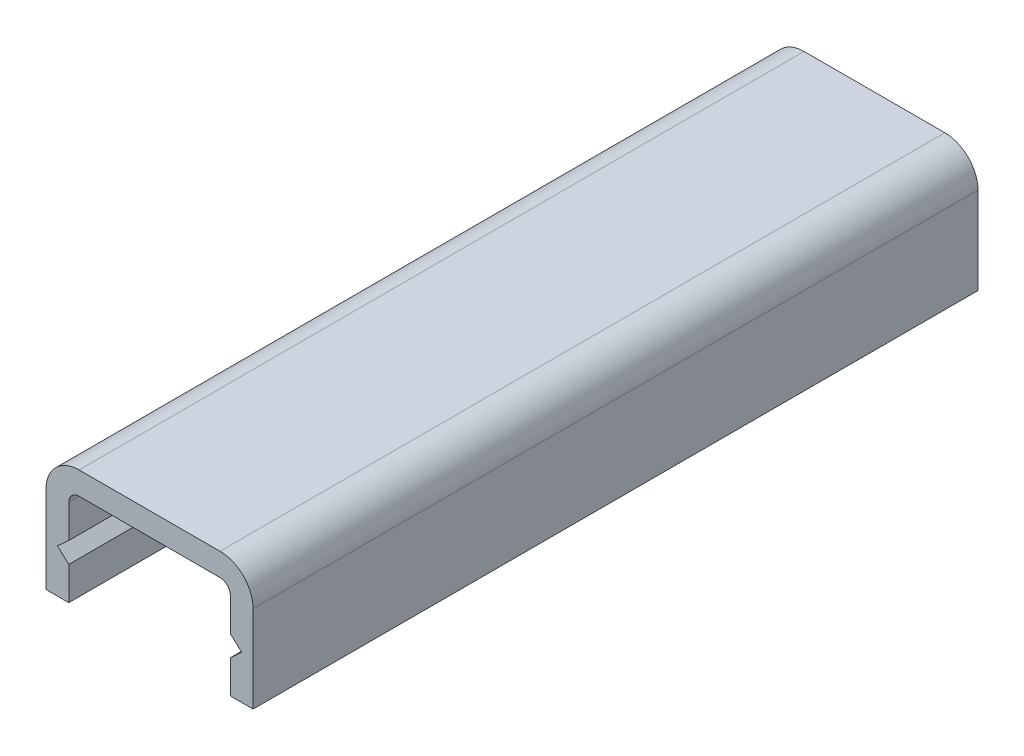
SolidWorks part; units mm, degrees
ref_plane "Plan de face" through (0, 0, 0) normal (0, 0, 1) x (1, 0, 0)
ref_plane "Plan de dessus" through (0, 0, 0) normal (0, 1, 0) x (1, 0, 0)
ref_plane "Plan de droite" through (0, 0, 0) normal (1, 0, 0) x (0, 0, -1)
sketch "Esquisse1" plane through (0, 0, 0) normal (0, 0, 1) x (1, 0, 0)
  line L0 (1.6, 5.8) -> (8.4, 5.8)
  line L1 (10, 4.2) -> (10, 0)
  line L2 (10, 0) -> (8.9, 0)
  line L3 (0, 4.2) -> (0, 0)
  line L4 (1.1, 2.6) -> (8.9, 2.6) construction
  line L5 (8.9, 4.2) -> (8.9, 2.6)
  line L6 (1.6, 4.7) -> (8.4, 4.7)
  line L7 (1.1, 4.2) -> (1.1, 2.6)
  line L8 (0, 0) -> (1.1, 0)
  line L9 (8.9, 4.7) -> (8.9, 1.1) construction
  line L10 (0, 5.8) -> (10, 5.8) construction
  line L11 (0, 5.8) -> (0, 0) construction
  line L12 (1.1, 4.7) -> (8.9, 4.7) construction
  line L13 (1.1, 4.7) -> (1.1, 0) construction
  line L14 (10, 5.8) -> (10, 0) construction
  line L15 (1.1, 1.6) -> (1.1, 0)
  line L16 (1.1, 1.6) -> (0.55, 2.1)
  line L17 (8.9, 1.6) -> (8.9, 0)
  line L18 (1.1, 2.6) -> (0.55, 2.1)
  line L19 (8.9, 2.6) -> (9.45, 2.1)
  line L20 (8.9, 1.6) -> (9.45, 2.1)
  line L21 (8.9, 1.1) -> (8.9, 1.1) construction
  line L22 (0.55, 2.1) -> (9.45, 2.1) construction
  line L23 (8.9, 1.6) -> (1.1, 1.6) construction
  line L24 (0, 0) -> (10, 0) construction
  arc A1 (1.6, 4.7) -> (1.1, 4.2) centre (1.6, 4.2) ccw
  arc A2 (8.9, 4.2) -> (8.4, 4.7) centre (8.4, 4.2) ccw
  arc A3 (8.4, 5.8) -> (10, 4.2) centre (8.4, 4.2) cw
  arc A4 (0, 4.2) -> (1.6, 5.8) centre (1.6, 4.2) cw
  dimension "D2" = 6.8
  dimension "D3" = 1.6
  dimension "D1" = 1.1
  dimension "D4" = 1.6
  dimension "D5" = 0.5
  dimension "D6" = 0.5
  dimension "D7" = 1.6
  dimension "D8" = 4.2
  dimension "D9" = 0.55
  dimension "D10" = 6.8
  dimension "D11" = 0.55
extrude "Extrusion1" add sketch "Esquisse1" along normal blind 35
